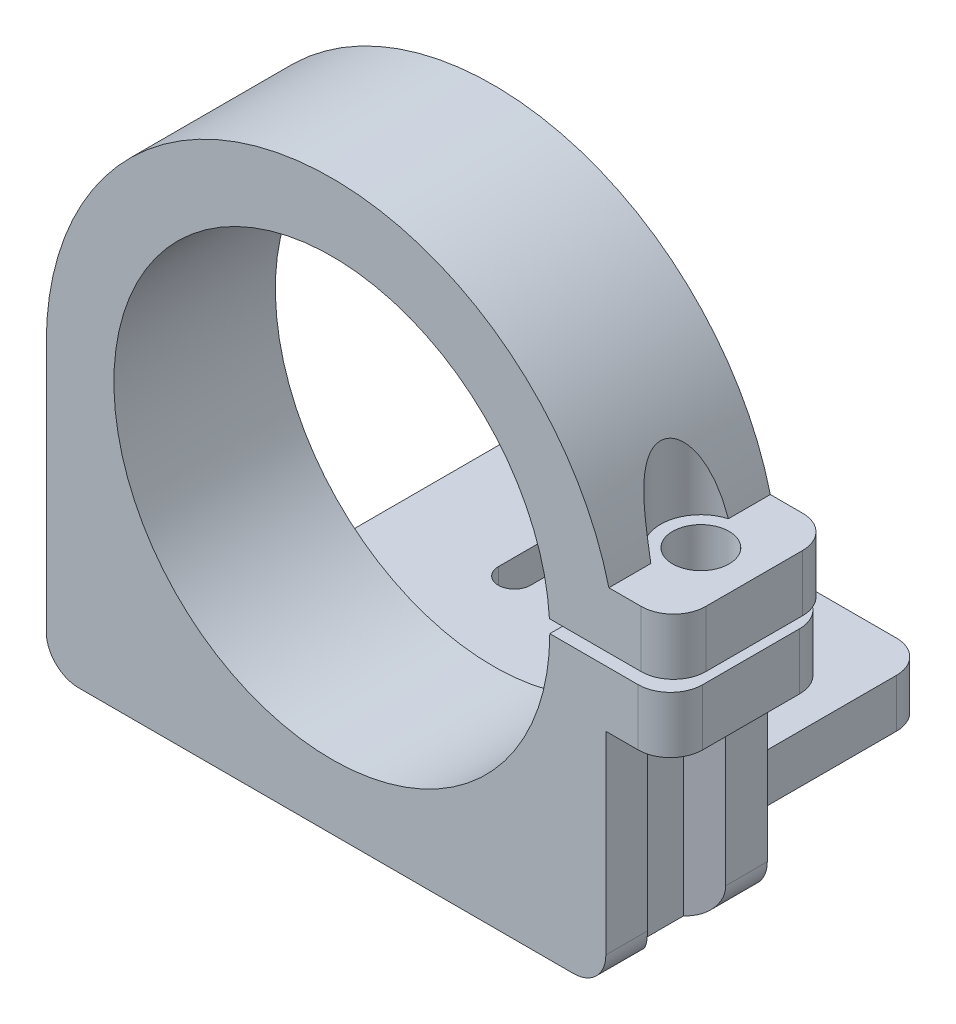
SolidWorks part; units mm, degrees
ref_plane "Alzado" through (0, 0, 0) normal (0, 0, 1) x (1, 0, 0)
ref_plane "Planta" through (0, 0, 0) normal (0, 1, 0) x (1, 0, 0)
ref_plane "Vista lateral" through (0, 0, 0) normal (1, 0, 0) x (0, 0, -1)
sketch "Croquis1" plane through (0, 0, 0) normal (0, 0, 1) x (1, 0, 0)
  line L0 (-17.6886, 0) -> (-17.6886, -17.5)
  line L1 (-17.6886, -17.5) -> (16.9715, -17.5)
  line L2 (16.9715, -17.5) -> (16.9715, -3.5)
  line L3 (13.5, 0) -> (20.9715, 0)
  line L4 (20.9715, 0) -> (20.9715, -3.5)
  line L5 (20.9715, -3.5) -> (16.9715, -3.5)
  line L6 (13.4768, 0.7917) -> (21.16, 0.7917)
  line L7 (21.16, 0.7917) -> (21.16, 4.2917)
  line L8 (21.16, 4.2917) -> (17.16, 4.2917)
  arc A0 (13.4768, 0.7917) -> (13.5, 0) centre (0, 0) ccw
  arc A2 (17.16, 4.2917) -> (-17.6886, 0) centre (0, 0) ccw
  dimension "D1" = 27
  dimension "D2" = 4
  dimension "D3" = 3.5
  dimension "D4" = 4
  dimension "D5" = 3.5
extrude "Saliente-Extruir1" add sketch "Croquis1" along normal blind 10
sketch "Croquis2" plane through (0, 0, 0) normal (0, 0, -1) x (-1, 0, 0)
  line L0 (17.6886, -17.5) -> (-16.9715, -17.5) construction
  line L1 (12.6886, -17.5) -> (-11.9715, -17.5)
  line L2 (12.6886, -17.5) -> (12.6886, -14.5)
  line L3 (12.6886, -14.5) -> (-11.9715, -14.5)
  line L4 (-11.9715, -17.5) -> (-11.9715, -14.5)
  line L5 (17.6886, 0) -> (17.6886, -17.5) construction
  line L6 (-16.9715, -17.5) -> (-16.9715, -3.5) construction
  dimension "D1" = 3
  dimension "D2" = 5
  dimension "D3" = 5
extrude "Saliente-Extruir2" add sketch "Croquis2" along normal blind 15
sketch "Croquis3" plane through (0, -17.5, 0) normal (0, -1, 0) x (1, 0, 0)
  line L0 (4.8114, -6.5) -> (4.8114, -11.5) construction
  line L1 (5.8114, -6.5) -> (5.8114, -11.5)
  line L2 (3.8114, -6.5) -> (3.8114, -11.5)
  line L3 (-5.1886, -6.5) -> (-5.1886, -11.5) construction
  line L4 (-4.1886, -6.5) -> (-4.1886, -11.5)
  line L5 (-6.1886, -6.5) -> (-6.1886, -11.5)
  line L8 (11.9715, -15) -> (-12.6886, -15) construction
  arc A0 (5.8114, -6.5) -> (3.8114, -6.5) centre (4.8114, -6.5) ccw
  arc A1 (3.8114, -11.5) -> (5.8114, -11.5) centre (4.8114, -11.5) ccw
  arc A2 (-4.1886, -6.5) -> (-6.1886, -6.5) centre (-5.1886, -6.5) ccw
  arc A3 (-6.1886, -11.5) -> (-4.1886, -11.5) centre (-5.1886, -11.5) ccw
  point P2 (4.8114, -9)
  point P7 (-5.1886, -9)
  dimension "D2" = 1
  dimension "D3" = 1
  dimension "D1" = 10
  dimension "D4" = 3.5
  dimension "D5" = 5
  dimension "D6" = 5
extrude "Cortar-Extruir1" cut sketch "Croquis3" against normal blind 15
fillet "Redondeo1" radius 2 8 edges at (16.9715, -17.5, 5) (-17.6886, -17.5, 5) (11.9715, -16, -15) (-12.6886, -16, -15) (21.16, 2.5417, 10) (20.9715, -1.75, 10) (20.9715, -1.75, 0) (21.16, 2.5417, 0)
sketch "Croquis4" plane through (0, 4.2917, 0) normal (0, 1, 0) x (1, 0, 0)
  circle A0 centre (17.8572, -5) radius 1.75
extrude "Cortar-Extruir2" cut sketch "Croquis4" against normal blind 25 and the other way blind 15
sketch "Croquis5" plane through (0, 4.2917, 0) normal (0, 1, 0) x (1, 0, 0)
  circle A0 centre (17.8572, -5) radius 2.5
extrude "Cortar-Extruir3" cut sketch "Croquis5" along normal blind 25
sketch "Croquis8" plane through (0, -3.5, 0) normal (0, -1, 0) x (1, 0, 0)
  line L1 (17.8572, 7.9374) -> (15.3133, 6.4687)
  line L2 (15.3133, 6.4687) -> (15.3133, 3.5313)
  line L3 (15.3133, 3.5313) -> (17.8572, 2.0626)
  line L4 (17.8572, 2.0626) -> (20.401, 3.5313)
  line L5 (20.401, 3.5313) -> (20.401, 6.4687)
  line L6 (20.401, 6.4687) -> (17.8572, 7.9374)
  circle A0 centre (17.8572, 5) radius 2.5439 construction
extrude "Cortar-Extruir4" cut sketch "Croquis8" along normal blind 25
